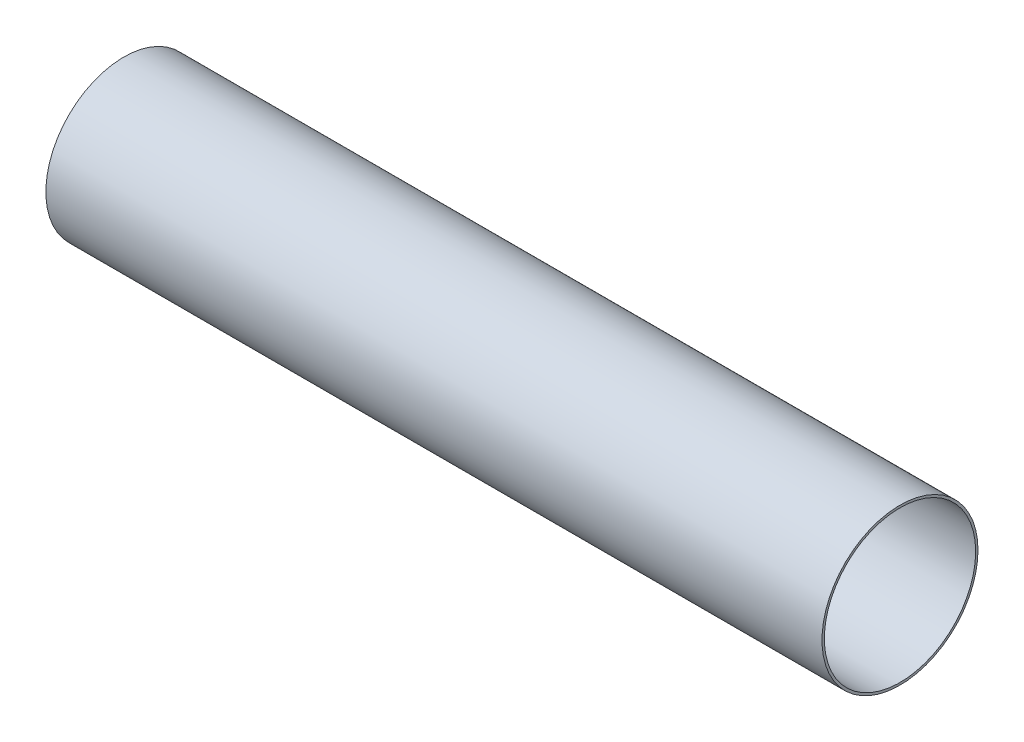
SolidWorks part; units mm, degrees
ref_plane "Front Plane" through (0, 0, 0) normal (1, 0, 0) x (0, 1, 0)
ref_plane "Top Plane" through (0, 0, 0) normal (0, 0, 1) x (0, 1, 0)
ref_plane "Right Plane" through (0, 0, 0) normal (0, 1, 0) x (-1, 0, 0)
sketch "Sketch1" plane through (0, 0, 0) normal (1, 0, 0) x (0, 1, 0)
  circle A0 centre (0, 0) radius 51.054
  circle A1 centre (0, 0) radius 49.53
  dimension "D1" = 99.06
  dimension "D2" = 102.108
extrude "Boss-Extrude1" add sketch "Sketch1" along normal blind 508
